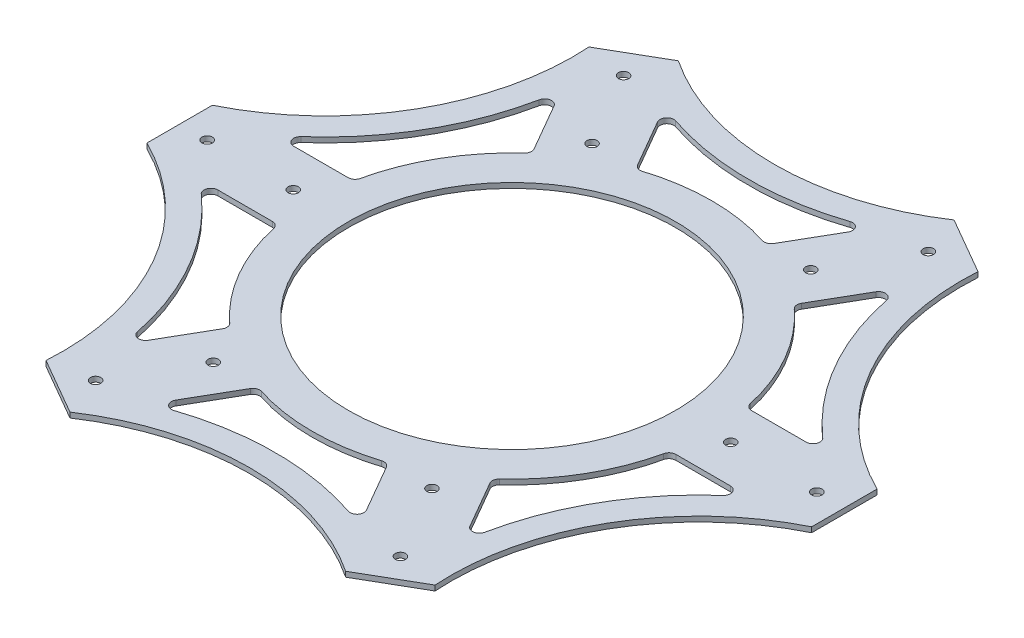
SolidWorks part; units mm, degrees
material "Thornel Mat VMA"
ref_plane "Спереди" through (0, 0, 0) normal (0, 0, 1) x (1, 0, 0)
ref_plane "Сверху" through (0, 0, 0) normal (0, 1, 0) x (1, 0, 0)
ref_plane "Справа" through (0, 0, 0) normal (1, 0, 0) x (0, 0, -1)
sketch "Эскиз1" plane through (0, 0, 0) normal (0, 1, 0) x (1, 0, 0)
  line L0 (-40.0228, 88.3215) -> (-48.25, 83.5715)
  line L1 (27.6737, 69.9323) -> (19.7611, 56.2272)
  line L2 (-96.5, 0) -> (0, 0) construction
  line L3 (-27.6737, 69.9323) -> (-19.7611, 56.2272)
  line L4 (-96.5, 9.5) -> (-96.5, 0)
  line L5 (40.0228, 88.3215) -> (48.25, 83.5715)
  line L6 (-46.7263, 58.9323) -> (-38.8136, 45.2272)
  line L7 (0, 0) -> (-48.25, 83.5715) construction
  line L8 (-48.25, 83.5715) -> (0, 0) construction
  line L9 (0, 0) -> (48.25, 83.5715) construction
  line L10 (-74.4, 11) -> (-58.5747, 11)
  line L11 (56.4772, 78.8215) -> (48.25, 83.5715)
  line L12 (74.4, 11) -> (58.5747, 11)
  line L13 (46.7263, 58.9323) -> (38.8136, 45.2272)
  line L14 (96.5, 9.5) -> (96.5, 0)
  line L15 (48.25, 83.5715) -> (0, 0) construction
  line L16 (0, 0) -> (96.5, 0) construction
  line L17 (96.5, -9.5) -> (96.5, 0)
  line L18 (46.7263, -58.9323) -> (38.8136, -45.2272)
  line L19 (-56.4772, 78.8215) -> (-48.25, 83.5715)
  line L20 (74.4, -11) -> (58.5747, -11)
  line L21 (56.4772, -78.8215) -> (48.25, -83.5715)
  line L22 (96.5, 0) -> (0, 0) construction
  line L23 (0, 0) -> (48.25, -83.5715) construction
  line L24 (40.0228, -88.3215) -> (48.25, -83.5715)
  line L25 (-27.6737, -69.9323) -> (-19.7611, -56.2272)
  line L26 (27.6737, -69.9323) -> (19.7611, -56.2272)
  line L27 (-40.0228, -88.3215) -> (-48.25, -83.5715)
  line L28 (48.25, -83.5715) -> (0, 0) construction
  line L29 (0, 0) -> (-48.25, -83.5715) construction
  line L30 (-56.4772, -78.8215) -> (-48.25, -83.5715)
  line L31 (-74.4, -11) -> (-58.5747, -11)
  line L32 (-46.7263, -58.9323) -> (-38.8136, -45.2272)
  line L33 (-96.5, -9.5) -> (-96.5, 0)
  line L34 (-48.25, -83.5715) -> (0, 0) construction
  line L35 (0, 0) -> (-96.5, 0) construction
  arc A0 (-96.5, 9.5) -> (-56.4772, 78.8215) centre (-128.467, 74.1705) ccw
  arc A1 (-75.7245, 14.4985) -> (-50.4184, 58.3301) centre (-128.467, 74.1705) ccw
  arc A2 (-75.7245, 14.4985) -> (-74.4, 11) centre (-74.4, 13) ccw
  arc A3 (-93.1766, 2.7766) -> (-48.9928, 79.305) centre (-128.467, 74.1705) ccw construction
  arc A4 (-39.1942, 42.753) -> (-56.6222, 12.5667) centre (0, 0) ccw
  arc A5 (-23.75, 41.1362) -> (-47.5, 0) centre (0, 0) ccw
  arc A6 (-58.5747, 11) -> (-56.6222, 12.5667) centre (-58.5747, 13) ccw
  arc A7 (-87, 0) -> (-90, 0) centre (-88.5, 0) ccw
  arc A8 (-62, 0) -> (-65, 0) centre (-63.5, 0) ccw
  arc A9 (-32.5, 56.2917) -> (-31, 53.6936) centre (-31.75, 54.9926) ccw
  arc A10 (-45, 77.9423) -> (-43.5, 75.3442) centre (-44.25, 76.6432) ccw
  arc A11 (-38.8136, 45.2272) -> (-39.1942, 42.753) centre (-40.5457, 44.2272) cw
  arc A12 (-50.4184, 58.3301) -> (-46.7263, 58.9323) centre (-48.4583, 57.9323) cw
  arc A13 (-40.0228, 88.3215) -> (40.0228, 88.3215) centre (0, 148.3409) ccw
  arc A14 (-25.3062, 72.8286) -> (25.3062, 72.8286) centre (0, 148.3409) ccw
  arc A15 (-25.3062, 72.8286) -> (-27.6737, 69.9323) centre (-25.9417, 70.9323) ccw
  arc A16 (17.4281, 55.3196) -> (-17.4281, 55.3196) centre (0, 0) ccw
  arc A17 (23.75, 41.1362) -> (-23.75, 41.1362) centre (0, 0) ccw
  arc A18 (-19.7611, 56.2272) -> (-17.4281, 55.3196) centre (-18.029, 57.2272) ccw
  arc A19 (-43.5, 75.3442) -> (-45, 77.9423) centre (-44.25, 76.6432) ccw
  arc A20 (-31, 53.6936) -> (-32.5, 56.2917) centre (-31.75, 54.9926) ccw
  arc A21 (32.5, 56.2917) -> (31, 53.6936) centre (31.75, 54.9926) ccw
  arc A22 (45, 77.9423) -> (43.5, 75.3442) centre (44.25, 76.6432) ccw
  arc A23 (19.7611, 56.2272) -> (17.4281, 55.3196) centre (18.029, 57.2272) cw
  arc A24 (25.3062, 72.8286) -> (27.6737, 69.9323) centre (25.9417, 70.9323) cw
  arc A25 (56.4772, 78.8215) -> (96.5, 9.5) centre (128.467, 74.1705) ccw
  arc A26 (50.4184, 58.3301) -> (75.7245, 14.4985) centre (128.467, 74.1705) ccw
  arc A27 (50.4184, 58.3301) -> (46.7263, 58.9323) centre (48.4583, 57.9323) ccw
  arc A28 (56.6222, 12.5667) -> (39.1942, 42.753) centre (0, 0) ccw
  arc A29 (47.5, 0) -> (23.75, 41.1362) centre (0, 0) ccw
  arc A30 (38.8136, 45.2272) -> (39.1942, 42.753) centre (40.5457, 44.2272) ccw
  arc A31 (43.5, 75.3442) -> (45, 77.9423) centre (44.25, 76.6432) ccw
  arc A32 (31, 53.6936) -> (32.5, 56.2917) centre (31.75, 54.9926) ccw
  arc A33 (65, 0) -> (62, 0) centre (63.5, 0) ccw
  arc A34 (90, 0) -> (87, 0) centre (88.5, 0) ccw
  arc A35 (58.5747, 11) -> (56.6222, 12.5667) centre (58.5747, 13) cw
  arc A36 (75.7245, 14.4985) -> (74.4, 11) centre (74.4, 13) cw
  arc A37 (96.5, -9.5) -> (56.4772, -78.8215) centre (128.467, -74.1705) ccw
  arc A38 (75.7245, -14.4985) -> (50.4184, -58.3301) centre (128.467, -74.1705) ccw
  arc A39 (75.7245, -14.4985) -> (74.4, -11) centre (74.4, -13) ccw
  arc A40 (39.1942, -42.753) -> (56.6222, -12.5667) centre (0, 0) ccw
  arc A41 (23.75, -41.1362) -> (47.5, 0) centre (0, 0) ccw
  arc A42 (58.5747, -11) -> (56.6222, -12.5667) centre (58.5747, -13) ccw
  arc A43 (87, 0) -> (90, 0) centre (88.5, 0) ccw
  arc A44 (62, 0) -> (65, 0) centre (63.5, 0) ccw
  arc A45 (32.5, -56.2917) -> (31, -53.6936) centre (31.75, -54.9926) ccw
  arc A46 (45, -77.9423) -> (43.5, -75.3442) centre (44.25, -76.6432) ccw
  arc A47 (38.8136, -45.2272) -> (39.1942, -42.753) centre (40.5457, -44.2272) cw
  arc A48 (50.4184, -58.3301) -> (46.7263, -58.9323) centre (48.4583, -57.9323) cw
  arc A49 (40.0228, -88.3215) -> (-40.0228, -88.3215) centre (0, -148.3409) ccw
  arc A50 (25.3062, -72.8286) -> (-25.3062, -72.8286) centre (0, -148.3409) ccw
  arc A51 (25.3062, -72.8286) -> (27.6737, -69.9323) centre (25.9417, -70.9323) ccw
  arc A52 (-17.4281, -55.3196) -> (17.4281, -55.3196) centre (0, 0) ccw
  arc A53 (-23.75, -41.1362) -> (23.75, -41.1362) centre (0, 0) ccw
  arc A54 (19.7611, -56.2272) -> (17.4281, -55.3196) centre (18.029, -57.2272) ccw
  arc A55 (43.5, -75.3442) -> (45, -77.9423) centre (44.25, -76.6432) ccw
  arc A56 (31, -53.6936) -> (32.5, -56.2917) centre (31.75, -54.9926) ccw
  arc A57 (-32.5, -56.2917) -> (-31, -53.6936) centre (-31.75, -54.9926) ccw
  arc A58 (-45, -77.9423) -> (-43.5, -75.3442) centre (-44.25, -76.6432) ccw
  arc A59 (-19.7611, -56.2272) -> (-17.4281, -55.3196) centre (-18.029, -57.2272) cw
  arc A60 (-25.3062, -72.8286) -> (-27.6737, -69.9323) centre (-25.9417, -70.9323) cw
  arc A61 (-56.4772, -78.8215) -> (-96.5, -9.5) centre (-128.467, -74.1705) ccw
  arc A62 (-50.4184, -58.3301) -> (-75.7245, -14.4985) centre (-128.467, -74.1705) ccw
  arc A63 (-50.4184, -58.3301) -> (-46.7263, -58.9323) centre (-48.4583, -57.9323) ccw
  arc A64 (-56.6222, -12.5667) -> (-39.1942, -42.753) centre (0, 0) ccw
  arc A65 (-47.5, 0) -> (-23.75, -41.1362) centre (0, 0) ccw
  arc A66 (-38.8136, -45.2272) -> (-39.1942, -42.753) centre (-40.5457, -44.2272) ccw
  arc A67 (-43.5, -75.3442) -> (-45, -77.9423) centre (-44.25, -76.6432) ccw
  arc A68 (-31, -53.6936) -> (-32.5, -56.2917) centre (-31.75, -54.9926) ccw
  arc A69 (-65, 0) -> (-62, 0) centre (-63.5, 0) ccw
  arc A70 (-90, 0) -> (-87, 0) centre (-88.5, 0) ccw
  arc A71 (-58.5747, -11) -> (-56.6222, -12.5667) centre (-58.5747, -13) cw
  arc A72 (-75.7245, -14.4985) -> (-74.4, -11) centre (-74.4, -13) cw
  point P0 (0, 0)
  point P14 (-31.4974, 35.5551)
  point P19 (-46.5403, 9.5)
  point P42 (0, 0)
  point P52 (15.0429, 45.0551)
  point P57 (-15.0429, 45.0551)
  point P77 (0, 0)
  point P87 (46.5403, 9.5)
  point P92 (31.4974, 35.5551)
  point P112 (0, 0)
  point P122 (31.4974, -35.5551)
  point P127 (46.5403, -9.5)
  point P147 (0, 0)
  point P157 (-15.0429, -45.0551)
  point P162 (15.0429, -45.0551)
  point P182 (0, 0)
  point P192 (-46.5403, -9.5)
  point P197 (-31.4974, -35.5551)
  point P217 (0, 0)
  dimension "D1" = 7.5
  dimension "D2" = 2
  dimension "D3" = 6
extrude "Бобышка-Вытянуть1" add sketch "Эскиз1" along normal blind 1.5
